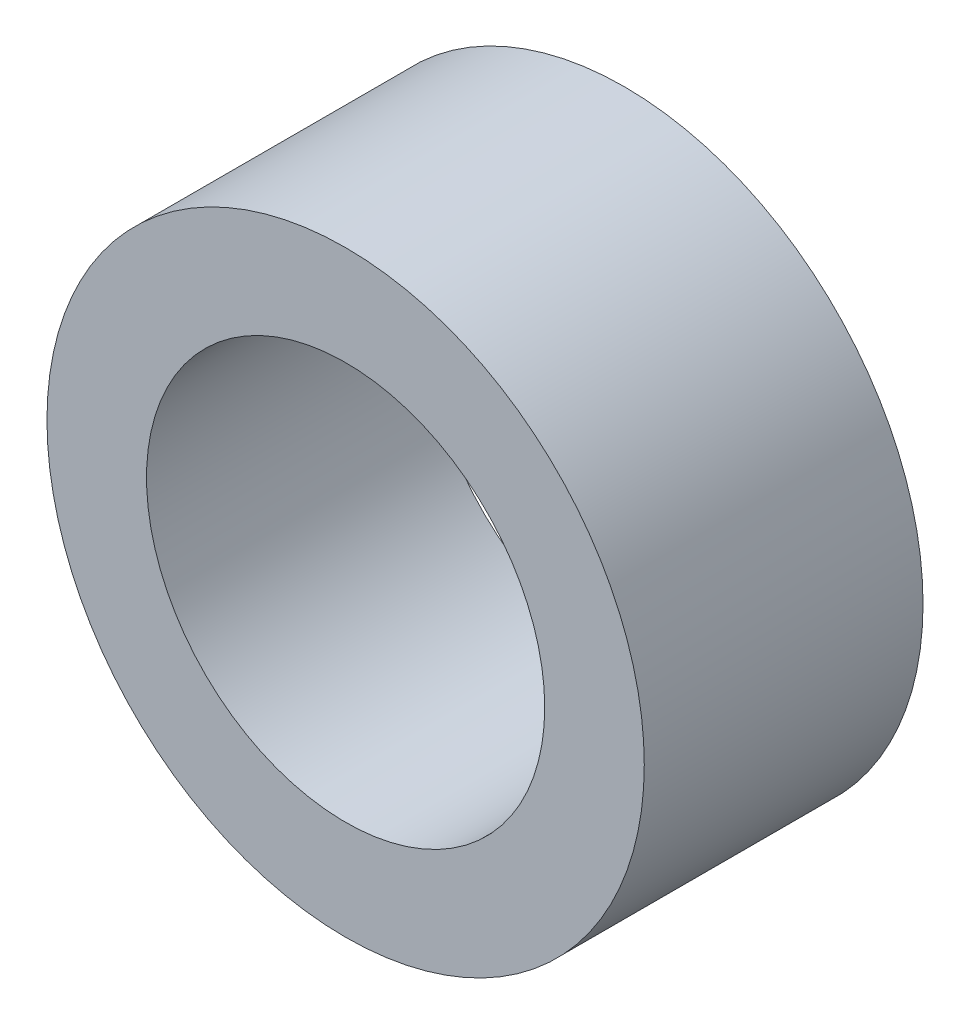
SolidWorks part; units mm, degrees
ref_plane "Front Plane" through (0, 0, 0) normal (0, 0, 1) x (1, 0, 0)
ref_plane "Top Plane" through (0, 0, 0) normal (0, 1, 0) x (1, 0, 0)
ref_plane "Right Plane" through (0, 0, 0) normal (1, 0, 0) x (0, 0, -1)
sketch "Sketch1" plane through (0, 0, 0) normal (0, 0, 1) x (1, 0, 0)
  circle A0 centre (0, 0) radius 20
  circle A1 centre (0, 0) radius 30
  dimension "D1" = 40
  dimension "D2" = 60
extrude "Boss-Extrude1" add sketch "Sketch1" along normal blind 28
